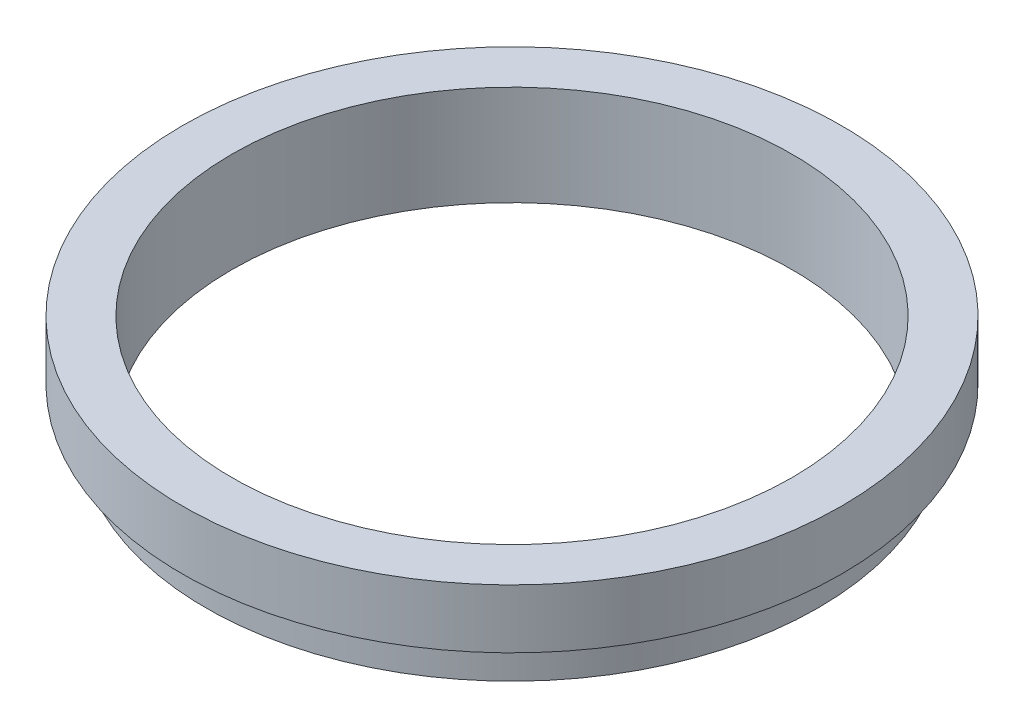
SolidWorks part; units mm, degrees
ref_plane "前视基准面" through (0, 0, 0) normal (0, 0, 1) x (1, 0, 0)
ref_plane "上视基准面" through (0, 0, 0) normal (0, 1, 0) x (1, 0, 0)
ref_plane "右视基准面" through (0, 0, 0) normal (1, 0, 0) x (0, 0, -1)
sketch "草图1" plane through (0, 0, 0) normal (0, 0, 1) x (1, 0, 0)
  line L0 (0, 16.886) -> (0, -24.4878) construction
  line L1 (23.8, -0.5455) -> (23.8, 7.9545)
  line L2 (28, 7.9545) -> (28, 2.9545)
  line L3 (23.8, 7.9545) -> (28, 7.9545)
  line L4 (25.4, 2.9545) -> (25.4, 1.9545)
  line L5 (25.4, 2.9545) -> (28, 2.9545)
  line L7 (26, 1.9545) -> (26, -0.5455)
  line L8 (25.4, 1.9545) -> (26, 1.9545)
  line L9 (23.8, -0.5455) -> (26, -0.5455)
  dimension "D1" = 23.8
  dimension "D2" = 28
  dimension "D3" = 5
  dimension "D4" = 8.5
  dimension "D5" = 25.4
  dimension "D6" = 1
  dimension "D7" = 26
revolve "旋转1" add sketch "草图1" angle 360 about L0
cosmetic thread "装饰螺纹线1"
cosmetic thread "装饰螺纹线2"
